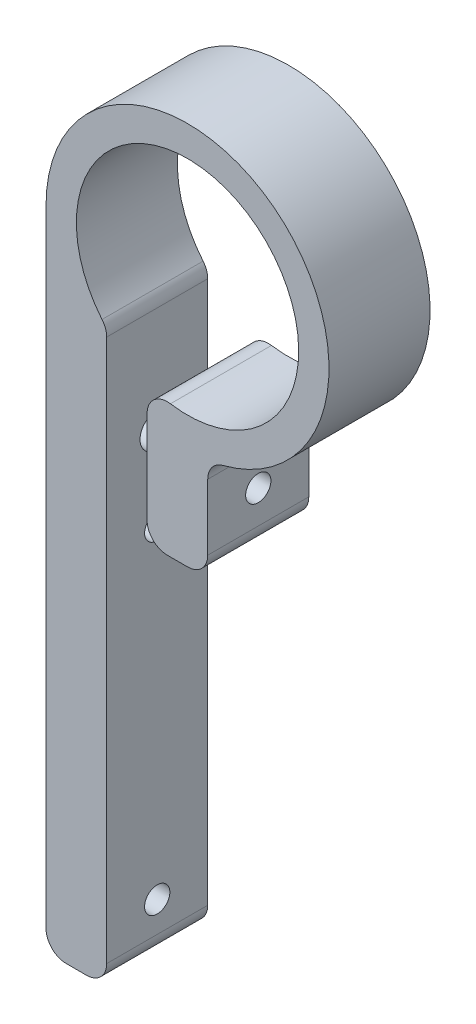
SolidWorks part; units mm, degrees
material "Сплав 2024"
ref_plane "Спереди" through (0, 0, 0) normal (0, 0, 1) x (1, 0, 0)
ref_plane "Сверху" through (0, 0, 0) normal (0, 1, 0) x (1, 0, 0)
ref_plane "Справа" through (0, 0, 0) normal (1, 0, 0) x (0, 0, -1)
sketch "Эскиз1" plane through (0, 0, 0) normal (0, 0, 1) x (1, 0, 0)
  line L0 (-14, 0) -> (-14, -64)
  line L1 (-8, -7.5498) -> (-8, -64)
  line L2 (-4, -10.247) -> (-4, -24)
  line L3 (2, -13.8564) -> (2, -24)
  line L4 (-4, -24) -> (2, -24)
  line L5 (-14, -64) -> (-8, -64)
  line L6 (-42.0107, -14) -> (30.8656, -14) construction
  arc A0 (-4, -10.247) -> (-8, -7.5498) centre (0, 0) ccw
  arc A1 (2, -13.8564) -> (-14, 0) centre (0, 0) ccw
  dimension "D1" = 22
  dimension "D2" = 28
  dimension "D3" = 6
  dimension "D4" = 4
  dimension "D5" = 6
  dimension "D6" = 50
  dimension "D7" = 10
extrude "Бобышка-Вытянуть1" add sketch "Эскиз1" along normal blind 10
fillet "Скругление1" radius 2 7 edges at (-14, -64, 5) (-8, -64, 5) (-4, -24, 5) (2, -24, 5) (2, -13.8564, 5) (-4, -10.247, 5) (-8, -7.5498, 5)
sketch "Эскиз2" plane through (2, 0, 0) normal (1, 0, 0) x (0, 0, -1)
  line L0 (-5, -15.4919) -> (-5, -22) construction
  line L1 (0, -15.4919) -> (-10, -15.4919) construction
  line L2 (-10, -22) -> (0, -22) construction
  line L3 (-10, -18.746) -> (0, -18.746) construction
  line L4 (-10, -22) -> (-10, -15.4919) construction
  line L5 (0, -22) -> (0, -15.4919) construction
hole_wizard "Цековка для винта с внутренним шестигранником M31" positions "Эскиз4" profile "Эскиз3" counterbore size "M3" standard "Ansi Metric" end condition up to next
sketch "Эскиз4" plane through (-14, 0, 0) normal (-1, 0, 0) x (0, 0, 1)
  line L0 (5, -15.4919) -> (5, -22) construction
  point P0 (5, -18.746)
sketch "Эскиз3" plane through (-14, -18.746, 5) normal (0, 1, 0) x (0, 0, 1)
  line L0 (0, 0) -> (0, 6)
  line L1 (0, 6) -> (1.7, 6)
  line L3 (1.7, 6) -> (1.7, 3)
  line L4 (1.7, 3) -> (3.25, 3)
  line L5 (3.25, 3) -> (3.25, 0)
  line L7 (3.25, 0) -> (0, 0)
  line L11 (0, -6.35) -> (0, 107.95) construction
  dimension "Диаметр сквозного отверстия" = 3.4
  dimension "Глубина сквозного отверстия" = 6
  dimension "Диаметр цековки" = 6.5
  dimension "Глубина цековки" = 3
hole_wizard "Отверстие обработанное метчиком M3x0.51" positions "Эскиз6" profile "Эскиз5" tap size "M3x0.5" standard "Ansi Metric" end condition up to next
sketch "Эскиз6" plane through (-4, 0, 0) normal (-1, 0, 0) x (0, 0, 1)
  line L0 (5, -15.4919) -> (5, -22) construction
  point P0 (5, -18.746)
sketch "Эскиз5" plane through (-4, -18.746, 5) normal (0, 1, 0) x (0, 0, 1)
  line L0 (0, 0) -> (0, 6)
  line L1 (0, 6) -> (1.25, 6)
  line L2 (1.25, 6) -> (1.25, 0)
  line L5 (1.25, 0) -> (0, 0)
  line L11 (0, -6.35) -> (0, 107.95) construction
  dimension "Диаметр проходного сверла" = 2.5
  dimension "Глубина проходного сверла" = 6
cosmetic thread "Отверстие резьбы1" parameters "D2"=3
sketch "Эскиз8" plane through (-14, 0, 0) normal (-1, 0, 0) x (0, 0, 1)
  line L0 (0, -59) -> (10, -59) construction
  line L1 (0, 0) -> (0, -62) construction
  line L2 (10, 0) -> (10, -62) construction
  line L3 (10, -27) -> (0, -27) construction
  line L4 (10, -64) -> (0, -64) construction
  line L5 (5, -62) -> (5, 0) construction
  line L6 (0, -62) -> (10, -62) construction
  line L7 (10, 0) -> (0, 0) construction
  dimension "D1" = 32
  dimension "D2" = 5
hole_wizard "Отверстие обработанное метчиком M3x0.52" positions "Эскиз10" profile "Эскиз9" tap size "M3x0.5" standard "Ansi Metric" end condition through all
sketch "Эскиз10" plane through (-14, 0, 0) normal (-1, 0, 0) x (0, 0, 1)
  line L0 (10, -27) -> (0, -27) construction
  line L1 (0, -59) -> (10, -59) construction
  point P0 (5, -27)
  point P4 (5, -59)
sketch "Эскиз9" plane through (-14, -27, 5) normal (0, 1, 0) x (0, 0, 1)
  line L0 (0, 0) -> (0, 28)
  line L1 (0, 28) -> (1.25, 28)
  line L2 (1.25, 28) -> (1.25, 0)
  line L5 (1.25, 0) -> (0, 0)
  line L11 (0, -6.35) -> (0, 107.95) construction
  dimension "Диаметр проходного сверла" = 2.5
  dimension "Глубина проходного сверла" = 28
cosmetic thread "Отверстие резьбы2" parameters "D2"=3
cosmetic thread "Отверстие резьбы3" parameters "D2"=3
